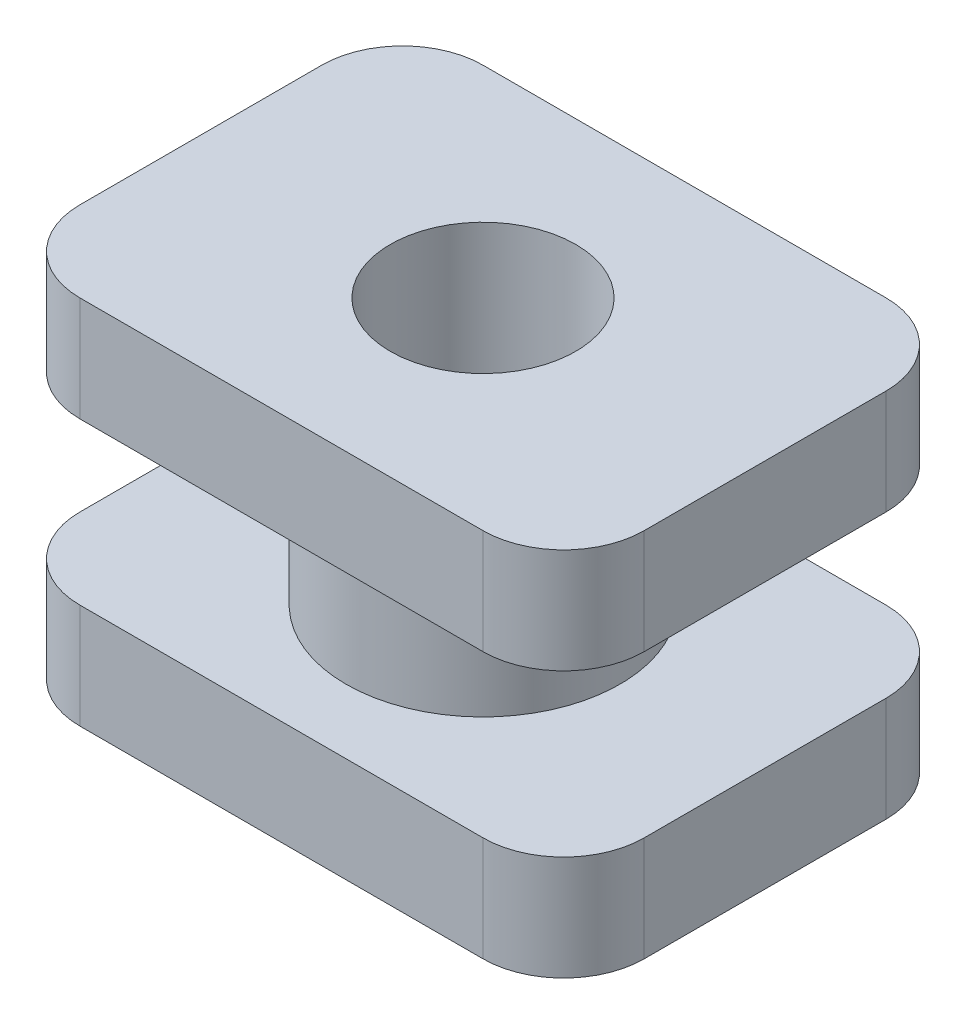
SolidWorks part; units mm, degrees
ref_plane "Front Plane" through (0, 0, 0) normal (0, 0, 1) x (1, 0, 0)
ref_plane "Top Plane" through (0, 0, 0) normal (0, 1, 0) x (1, 0, 0)
ref_plane "Right Plane" through (0, 0, 0) normal (1, 0, 0) x (0, 0, -1)
sketch "Sketch1" plane through (0, 0, 0) normal (0, 1, 0) x (1, 0, 0)
  circle A0 centre (0, 0) radius 2.159
  dimension "D1" = 4.318
extrude "Boss-Extrude1" add sketch "Sketch1" along normal blind 2.54
sketch "Sketch2" plane through (0, 2.54, 0) normal (0, 1, 0) x (1, 0, 0)
  line L1 (-4.445, -3.175) -> (4.445, -3.175)
  line L2 (-4.445, -3.175) -> (-4.445, 3.175)
  line L3 (-4.445, 3.175) -> (4.445, 3.175)
  line L4 (4.445, -3.175) -> (4.445, 3.175)
  line L5 (-4.445, -3.175) -> (4.445, 3.175) construction
  line L6 (-4.445, 3.175) -> (4.445, -3.175) construction
  point P0 (0, 0)
  dimension "D1" = 6.35
  dimension "D2" = 8.89
extrude "Boss-Extrude2" add sketch "Sketch2" along normal blind 1.651
sketch "Sketch3" plane through (0, 0, 0) normal (0, -1, 0) x (-1, 0, 0)
  line L1 (-4.445, -3.175) -> (4.445, -3.175)
  line L2 (-4.445, -3.175) -> (-4.445, 3.175)
  line L3 (-4.445, 3.175) -> (4.445, 3.175)
  line L4 (4.445, -3.175) -> (4.445, 3.175)
  line L5 (-4.445, -3.175) -> (4.445, 3.175) construction
  line L6 (-4.445, 3.175) -> (4.445, -3.175) construction
  point P0 (0, 0)
  dimension "D1" = 6.35
  dimension "D2" = 8.89
extrude "Boss-Extrude3" add sketch "Sketch3" along normal blind 1.651
sketch "Sketch4" plane through (0, 4.191, 0) normal (0, 1, 0) x (1, 0, 0)
  circle A0 centre (0, 0) radius 1.4605
  dimension "D1" = 2.921
extrude "Cut-Extrude1" cut sketch "Sketch4" against normal through all
fillet "Fillet1" radius 1.27 8 edges at (-4.445, -0.8255, 3.175) (-4.445, -0.8255, -3.175) (4.445, -0.8255, -3.175) (4.445, -0.8255, 3.175) (4.445, 3.3655, 3.175) (4.445, 3.3655, -3.175) (-4.445, 3.3655, 3.175) (-4.445, 3.3655, -3.175)
